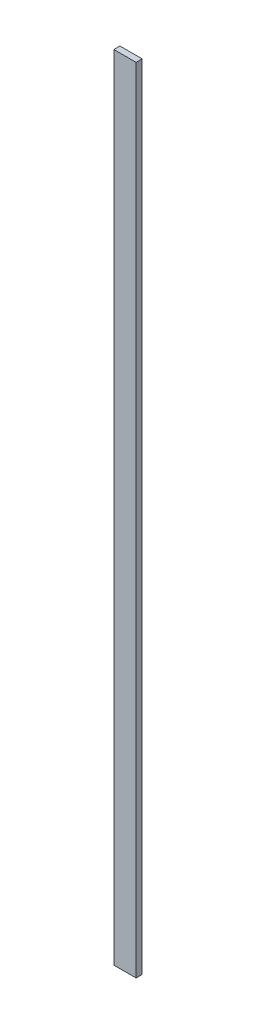
SolidWorks part; units mm, degrees
material "Oak"
ref_plane "Front Plane" through (0, 0, 0) normal (0, 0, 1) x (1, 0, 0)
ref_plane "Top Plane" through (0, 0, 0) normal (0, 1, 0) x (1, 0, 0)
ref_plane "Right Plane" through (0, 0, 0) normal (1, 0, 0) x (0, 0, -1)
sketch "Sketch1" plane through (0, 0, 0) normal (0, 1, 0) x (1, 0, 0)
  line L1 (-69.85, -19.05) -> (69.85, -19.05)
  line L2 (-69.85, -19.05) -> (-69.85, 19.05)
  line L3 (-69.85, 19.05) -> (69.85, 19.05)
  line L4 (69.85, -19.05) -> (69.85, 19.05)
  line L5 (-69.85, -19.05) -> (69.85, 19.05) construction
  line L6 (-69.85, 19.05) -> (69.85, -19.05) construction
  point P0 (0, 0)
  dimension "D1" = 38.1
  dimension "D2" = 139.7
extrude "Boss-Extrude1" add sketch "Sketch1" along normal blind 4978.4 contours L4 L3 L2 L1
